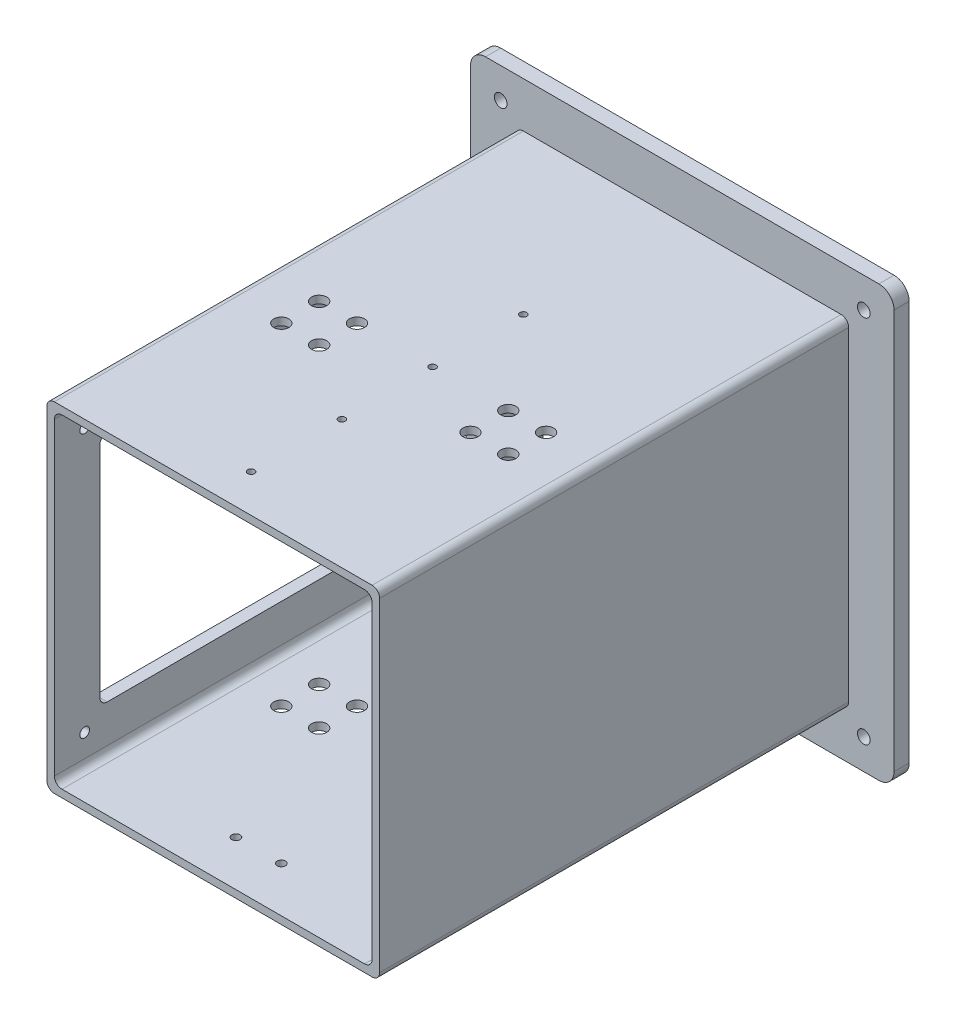
SolidWorks part; units mm, degrees
ref_plane "前视基准面" through (0, 0, 0) normal (0, 0, 1) x (1, 0, 0)
ref_plane "上视基准面" through (0, 0, 0) normal (0, 1, 0) x (1, 0, 0)
ref_plane "右视基准面" through (0, 0, 0) normal (1, 0, 0) x (0, 0, -1)
sketch "草图1" plane through (0, 0, 0) normal (0, 0, 1) x (1, 0, 0)
  line L1 (-105, -107.125) -> (105, -107.125)
  line L2 (-105, -107.125) -> (-105, 107.125)
  line L3 (-105, 107.125) -> (105, 107.125)
  line L4 (105, -107.125) -> (105, 107.125)
  line L5 (-105, -107.125) -> (105, 107.125) construction
  line L6 (-105, 107.125) -> (105, -107.125) construction
  line L7 (-110, -112.125) -> (110, -112.125)
  line L8 (-110, -112.125) -> (-110, 112.125)
  line L9 (-110, 112.125) -> (110, 112.125)
  line L10 (110, -112.125) -> (110, 112.125)
  line L11 (-110, -112.125) -> (110, 112.125) construction
  line L12 (-110, 112.125) -> (110, -112.125) construction
  point P0 (0, 0)
  point P6 (0, 0)
  dimension "D1" = 210
  dimension "D2" = 214.25
  dimension "D3" = 5
  dimension "D4" = 5
extrude "凸台-拉伸1" add sketch "草图1" along normal blind 310
sketch "草图2" plane through (0, 0, 0) normal (0, 0, -1) x (-1, 0, 0)
  line L0 (-110, 112.125) -> (110, 112.125) construction
  line L1 (-140, -142.125) -> (140, -142.125)
  line L2 (-140, -142.125) -> (-140, 142.125)
  line L3 (-140, 142.125) -> (140, 142.125)
  line L4 (140, -142.125) -> (140, 142.125)
  line L5 (-140, -142.125) -> (140, 142.125) construction
  line L6 (-140, 142.125) -> (140, -142.125) construction
  line L7 (-110, -112.125) -> (-110, 112.125) construction
  line L8 (105, 107.125) -> (105, -107.125) construction
  line L9 (105, -107.125) -> (-105, -107.125) construction
  line L10 (-105, -107.125) -> (-105, 107.125) construction
  line L11 (-105, 107.125) -> (105, 107.125) construction
  line L12 (105, 107.125) -> (105, -107.125)
  line L13 (105, -107.125) -> (-105, -107.125)
  line L14 (-105, -107.125) -> (-105, 107.125)
  line L15 (-105, 107.125) -> (105, 107.125)
  point P0 (0, 0)
  dimension "D1" = 30
  dimension "D2" = 30
extrude "凸台-拉伸2" add sketch "草图2" along normal blind 10
fillet "圆角1" radius 5 4 edges at (110, 112.125, 155) (110, -112.125, 155) (-110, -112.125, 155) (-110, 112.125, 155)
fillet "圆角2" radius 5 4 edges at (105, 107.125, 150) (-105, 107.125, 150) (105, -107.125, 150) (-105, -107.125, 150)
fillet "圆角3" radius 10 4 edges at (-140, 142.125, -5) (140, 142.125, -5) (140, -142.125, -5) (-140, -142.125, -5)
hole_wizard "Ø8.4 (8.4) 直径孔1" positions "草图3" profile "草图4" hole size "Ø8.4" standard "GB" end condition through all
sketch "草图3" plane through (0, 0, 0) normal (0, 0, 1) x (1, 0, 0)
  line L0 (130, -142.125) -> (-130, -142.125) construction
  line L1 (140, 132.125) -> (140, -132.125) construction
  line L2 (-140, -132.125) -> (-140, 132.125) construction
  line L3 (-130, 142.125) -> (130, 142.125) construction
  point P0 (120, 122.125)
  point P3 (120, -122.125)
  point P6 (-120, -122.125)
  point P10 (-120, 122.125)
  dimension "D1" = 20
  dimension "D2" = 20
  dimension "D3" = 20
  dimension "D4" = 20
  dimension "D5" = 20
  dimension "D6" = 20
  dimension "D7" = 20
  dimension "D8" = 20
sketch "草图4" plane through (120, 122.125, 0) normal (1, 0, 0) x (0, -1, 0)
  line L0 (0, 0) -> (0, 10)
  line L1 (0, 10) -> (4.2, 10)
  line L2 (4.2, 10) -> (4.2, 0)
  line L5 (4.2, 0) -> (0, 0)
  line L11 (0, -6.35) -> (0, 107.95) construction
  dimension "通孔孔直径" = 8.4
  dimension "通孔孔深度" = 10
sketch "草图18" plane through (0, 112.125, 0) normal (0, 1, 0) x (1, 0, 0)
  line L0 (105, -310) -> (-105, -310) construction
  line L1 (-105, 0) -> (-105, -310) construction
  line L2 (105, -310) -> (105, 0) construction
  point P0 (-75, -165)
  point P1 (-75, -190)
  point P2 (-50, -190)
  point P3 (-50, -165)
  point P5 (50, -190)
  point P6 (75, -190)
  point P8 (75, -165)
  point P16 (50, -165)
  dimension "D1" = 25
  dimension "D2" = 25
  dimension "D3" = 35.3553
  dimension "D4" = 25
  dimension "D5" = 35.3553
  dimension "D6" = 25
  dimension "D7" = 30
  dimension "D8" = 30
  dimension "D9" = 25
  dimension "D10" = 25
  dimension "D11" = 25
  dimension "D12" = 25
  dimension "D13" = 120
  dimension "D14" = 120
  dimension "D15" = 35.3553
  dimension "D16" = 55
hole_wizard "大小mm 暗销孔11" positions "草图33" profile "草图34" hole size "Ø10.0" standard "GB" end condition through all
sketch "草图33" plane through (0, 112.125, 0) normal (0, 1, 0) x (1, 0, 0)
  point P0 (-75, -165)
  point P3 (-50, -165)
  point P6 (-50, -190)
  point P9 (-75, -190)
  point P12 (50, -190)
  point P15 (50, -165)
  point P18 (75, -165)
  point P21 (75, -190)
sketch "草图34" plane through (-75, 112.125, 165) normal (1, 0, 0) x (0, 0, 1)
  line L0 (0, 0) -> (0, 254.25)
  line L1 (0, 254.25) -> (5, 254.25)
  line L2 (5, 254.25) -> (5, 0)
  line L5 (5, 0) -> (0, 0)
  line L11 (0, -6.35) -> (0, 107.95) construction
  dimension "通孔孔直径" = 10
  dimension "通孔孔深度" = 254.25
sketch "草图35" plane through (0, -112.125, 0) normal (0, -1, 0) x (1, 0, 0)
  line L0 (130, 0) -> (-130, 0) construction
  line L2 (-105, 0) -> (105, 0) construction
  line L3 (105, 0) -> (105, 310) construction
  line L4 (-105, 310) -> (-105, 0) construction
  point P0 (15, 280)
  point P1 (19, 105.5)
  point P2 (-19, 105.5)
  point P4 (-15, 280)
  dimension "D1" = 90
  dimension "D2" = 38
  dimension "D4" = 19
  dimension "D5" = 280
  dimension "D6" = 280
  dimension "D7" = 105.5
  dimension "D8" = 105.5
  dimension "D9" = 90
sketch "草图38" plane through (0, 112.125, 0) normal (0, 1, 0) x (1, 0, 0)
  line L0 (-105, 0) -> (-105, -310) construction
  line L2 (105, 0) -> (-105, 0) construction
  point P0 (0, -105)
  point P1 (0, -165)
  point P2 (0, -285)
  point P3 (0, -225)
  dimension "D1" = 105
  dimension "D2" = 60
  dimension "D3" = 60
  dimension "D4" = 60
  dimension "D5" = 105
  dimension "D6" = 105
  dimension "D7" = 105
  dimension "D8" = 105
hole_wizard "Ø4.5 (4.5) 直径孔1" positions "草图39" profile "草图40" hole size "Ø4.5" standard "GB" end condition up to next
sketch "草图39" plane through (0, 112.125, 0) normal (0, 1, 0) x (1, 0, 0)
  point P0 (0, -105)
  point P3 (0, -165)
  point P6 (0, -225)
  point P9 (0, -285)
sketch "草图40" plane through (0, 112.125, 105) normal (1, 0, 0) x (0, 0, 1)
  line L0 (0, 0) -> (0, 5)
  line L1 (0, 5) -> (2.25, 5)
  line L2 (2.25, 5) -> (2.25, 0)
  line L5 (2.25, 0) -> (0, 0)
  line L11 (0, -6.35) -> (0, 107.95) construction
  dimension "通孔孔直径" = 4.5
  dimension "通孔孔深度" = 5
hole_wizard "Ø6.6 (6.6) 直径孔1" positions "草图41" profile "草图42" hole size "Ø6.6" standard "GB" end condition up to next
sketch "草图41" plane through (0, -112.125, 0) normal (0, -1, 0) x (-1, 0, 0)
  point P0 (19, -105.5)
  point P3 (-19, -105.5)
sketch "草图42" plane through (-19, -112.125, 105.5) normal (1, 0, 0) x (0, 0, -1)
  line L0 (0, 0) -> (0, 5)
  line L1 (0, 5) -> (3.3, 5)
  line L2 (3.3, 5) -> (3.3, 0)
  line L5 (3.3, 0) -> (0, 0)
  line L11 (0, -6.35) -> (0, 107.95) construction
  dimension "通孔孔直径" = 6.6
  dimension "通孔孔深度" = 5
hole_wizard "Ø5.5 (5.5) 直径孔1" positions "草图43" profile "草图44" hole size "Ø5.5" standard "GB" end condition up to next
sketch "草图43" plane through (0, -112.125, 0) normal (0, -1, 0) x (-1, 0, 0)
  point P0 (15, -280)
  point P3 (-15, -280)
sketch "草图44" plane through (-15, -112.125, 280) normal (1, 0, 0) x (0, 0, -1)
  line L0 (0, 0) -> (0, 5)
  line L1 (0, 5) -> (2.75, 5)
  line L2 (2.75, 5) -> (2.75, 0)
  line L5 (2.75, 0) -> (0, 0)
  line L11 (0, -6.35) -> (0, 107.95) construction
  dimension "通孔孔直径" = 5.5
  dimension "通孔孔深度" = 5
sketch "草图45" plane through (-110, 0, 0) normal (-1, 0, 0) x (0, 0, 1)
  line L0 (310, 107.125) -> (0, 107.125) construction
  line L1 (280, -77.125) -> (30, -77.125)
  line L2 (280, -77.125) -> (280, 77.125)
  line L3 (280, 77.125) -> (30, 77.125)
  line L4 (30, -77.125) -> (30, 77.125)
  line L5 (280, -77.125) -> (30, 77.125) construction
  line L6 (280, 77.125) -> (30, -77.125) construction
  line L7 (0, -107.125) -> (310, -107.125) construction
  line L8 (0, -132.125) -> (0, 132.125) construction
  line L9 (310, 107.125) -> (310, -107.125) construction
  point P0 (155, 0)
  dimension "D1" = 30
  dimension "D2" = 30
  dimension "D3" = 30
  dimension "D4" = 30
extrude "切除-拉伸1" cut sketch "草图45" against normal up to next
fillet "圆角4" radius 5 4 edges at (-107.5, -77.125, 30) (-107.5, -77.125, 280) (-107.5, 77.125, 280) (-107.5, 77.125, 30)
sketch "草图49" plane through (-110, 0, 0) normal (-1, 0, 0) x (0, 0, 1)
  line L0 (275, 77.125) -> (35, 77.125) construction
  line L1 (27, 80.125) -> (283, 80.125)
  line L2 (27, 80.125) -> (27, -80.125)
  line L3 (27, -80.125) -> (283, -80.125)
  line L4 (283, 80.125) -> (283, -80.125)
  line L5 (35, -77.125) -> (275, -77.125) construction
  line L6 (30, 72.125) -> (30, -72.125) construction
  line L7 (280, -72.125) -> (280, 72.125) construction
  line L8 (280, -72.125) -> (280, 72.125)
  line L9 (35, -77.125) -> (275, -77.125)
  line L10 (30, 72.125) -> (30, -72.125)
  line L11 (275, 77.125) -> (35, 77.125)
  arc A0 (280, 72.125) -> (275, 77.125) centre (275, 72.125) ccw construction
  arc A1 (275, -77.125) -> (280, -72.125) centre (275, -72.125) ccw construction
  arc A2 (30, -72.125) -> (35, -77.125) centre (35, -72.125) ccw construction
  arc A3 (35, 77.125) -> (30, 72.125) centre (35, 72.125) ccw construction
  arc A4 (280, 72.125) -> (275, 77.125) centre (275, 72.125) ccw
  arc A5 (275, -77.125) -> (280, -72.125) centre (275, -72.125) ccw
  arc A6 (30, -72.125) -> (35, -77.125) centre (35, -72.125) ccw
  arc A7 (35, 77.125) -> (30, 72.125) centre (35, 72.125) ccw
  dimension "D1" = 3
  dimension "D2" = 3
  dimension "D3" = 3
  dimension "D4" = 3
extrude "凸台-拉伸3" add sketch "草图49" along normal blind 3
fillet "圆角5" radius 5 4 edges at (-111.5, 80.125, 27) (-111.5, -80.125, 27) (-111.5, -80.125, 283) (-111.5, 80.125, 283)
sketch "草图50" plane through (0, 0, -10) normal (0, 0, -1) x (-1, 0, 0)
  line L0 (100, 107.125) -> (-100, 107.125) construction
  line L1 (108, -110.125) -> (-108, -110.125)
  line L2 (108, -110.125) -> (108, 110.125)
  line L3 (108, 110.125) -> (-108, 110.125)
  line L4 (-108, -110.125) -> (-108, 110.125)
  line L5 (108, -110.125) -> (-108, 110.125) construction
  line L6 (108, 110.125) -> (-108, -110.125) construction
  line L7 (-105, 102.125) -> (-105, -102.125) construction
  line L8 (-100, -107.125) -> (100, -107.125) construction
  line L9 (105, -102.125) -> (105, 102.125) construction
  line L10 (-100, -107.125) -> (100, -107.125)
  line L11 (105, -102.125) -> (105, 102.125)
  line L12 (100, 107.125) -> (-100, 107.125)
  line L13 (-105, 102.125) -> (-105, -102.125)
  arc A0 (-105, -102.125) -> (-100, -107.125) centre (-100, -102.125) ccw construction
  arc A1 (100, -107.125) -> (105, -102.125) centre (100, -102.125) ccw construction
  arc A2 (105, 102.125) -> (100, 107.125) centre (100, 102.125) ccw construction
  arc A3 (-100, 107.125) -> (-105, 102.125) centre (-100, 102.125) ccw construction
  arc A4 (-105, -102.125) -> (-100, -107.125) centre (-100, -102.125) ccw
  arc A5 (100, -107.125) -> (105, -102.125) centre (100, -102.125) ccw
  arc A6 (105, 102.125) -> (100, 107.125) centre (100, 102.125) ccw
  arc A7 (-100, 107.125) -> (-105, 102.125) centre (-100, 102.125) ccw
  point P0 (0, 0)
  dimension "D1" = 3
  dimension "D2" = 3
extrude "凸台-拉伸4" add sketch "草图50" along normal blind 3
fillet "圆角6" radius 5 4 edges at (-108, 110.125, -11.5) (-108, -110.125, -11.5) (108, -110.125, -11.5) (108, 110.125, -11.5)
sketch "草图52" plane through (-110, 0, 0) normal (-1, 0, 0) x (0, 0, 1)
  line L0 (278, 80.125) -> (32, 80.125) construction
  line L1 (27, 75.125) -> (27, -75.125) construction
  line L2 (283, -75.125) -> (283, 75.125) construction
  line L3 (278, 80.125) -> (32, 80.125) construction
  line L4 (283, -75.125) -> (283, 75.125) construction
  line L5 (32, -80.125) -> (278, -80.125) construction
  point P0 (20, 87.125)
  point P1 (20, -87.125)
  point P2 (290, -87.125)
  point P3 (290, 87.125)
  dimension "D1" = 7
  dimension "D2" = 7
  dimension "D3" = 7
  dimension "D4" = 7
  dimension "D5" = 7
  dimension "D6" = 7
  dimension "D7" = 7
  dimension "D8" = 7
hole_wizard "Ø6.4 (6.4) 直径孔1" positions "草图53" profile "草图54" hole size "Ø6.4" standard "GB" end condition up to next
sketch "草图53" plane through (-110, 0, 0) normal (-1, 0, 0) x (0, 0, 1)
  point P0 (20, 87.125)
  point P3 (20, -87.125)
  point P6 (290, -87.125)
  point P9 (290, 87.125)
sketch "草图54" plane through (-110, 87.125, 20) normal (0, 1, 0) x (0, 0, 1)
  line L0 (0, 0) -> (0, 5)
  line L1 (0, 5) -> (3.2, 5)
  line L2 (3.2, 5) -> (3.2, 0)
  line L5 (3.2, 0) -> (0, 0)
  line L11 (0, -6.35) -> (0, 107.95) construction
  dimension "通孔孔直径" = 6.4
  dimension "通孔孔深度" = 5
sketch "草图55" plane through (0, -107.125, 0) normal (0, 1, 0) x (1, 0, 0)
  line L1 (-103, 10) -> (103, 10) construction
  line L3 (-105, 0) -> (-105, -310) construction
  line L4 (105, -310) -> (105, 0) construction
  point P0 (15, -41.55)
  point P1 (15, -11.55)
  point P2 (-15, -11.55)
  point P3 (-15, -41.55)
  point P6 (0, 0)
  point P7 (0, 0)
  dimension "D1" = 51.55
  dimension "D2" = 90
  dimension "D3" = 90
  dimension "D4" = 30
hole_wizard "Ø4.2 (4.2) 直径孔1" positions "草图56" profile "草图57" hole size "Ø4.2" standard "GB" end condition up to next
sketch "草图56" plane through (0, -107.125, 0) normal (0, 1, 0) x (1, 0, 0)
  point P0 (-15, -11.55)
  point P3 (15, -11.55)
  point P6 (15, -41.55)
  point P9 (-15, -41.55)
sketch "草图57" plane through (-15, -107.125, 11.55) normal (1, 0, 0) x (0, 0, 1)
  line L0 (0, 0) -> (0, 5)
  line L1 (0, 5) -> (2.1, 5)
  line L2 (2.1, 5) -> (2.1, 0)
  line L5 (2.1, 0) -> (0, 0)
  line L11 (0, -6.35) -> (0, 107.95) construction
  dimension "通孔孔直径" = 4.2
  dimension "通孔孔深度" = 5
